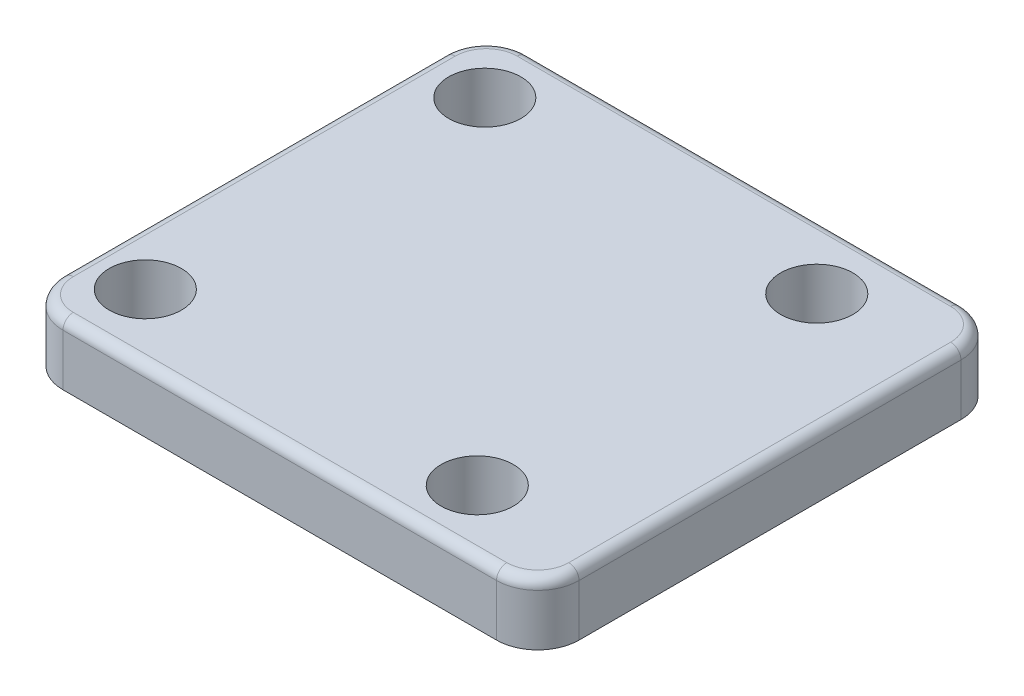
SolidWorks part; units mm, degrees
ref_plane "Front Plane" through (0, 0, 0) normal (0, 0, 1) x (1, 0, 0)
ref_plane "Top Plane" through (0, 0, 0) normal (0, 1, 0) x (1, 0, 0)
ref_plane "Right Plane" through (0, 0, 0) normal (1, 0, 0) x (0, 0, -1)
sketch "Sketch1" plane through (0, 0, 0) normal (0, 1, 0) x (1, 0, 0)
  line L0 (0, 0) -> (-22, 22.5)
  line L1 (-18, 22.5) -> (24, 22.5)
  line L2 (-22, 18.5) -> (-22, -18.5)
  line L3 (-18, -22.5) -> (24, -22.5)
  line L4 (28, 18.5) -> (28, -18.5)
  circle A0 centre (0, 0) radius 23 construction
  circle A1 centre (-16.0797, 16.4452) radius 3.5
  circle A2 centre (0, 0) radius 23 construction
  circle A3 centre (16.4452, 16.0797) radius 3.5
  circle A4 centre (0, 0) radius 23 construction
  circle A5 centre (16.0797, -16.4452) radius 3.5
  circle A6 centre (0, 0) radius 23 construction
  circle A7 centre (-16.4452, -16.0797) radius 3.5
  arc A8 (-22, -18.5) -> (-18, -22.5) centre (-18, -18.5) ccw
  arc A9 (24, -22.5) -> (28, -18.5) centre (24, -18.5) ccw
  arc A10 (24, 22.5) -> (28, 18.5) centre (24, 18.5) cw
  arc A11 (-18, 22.5) -> (-22, 18.5) centre (-18, 18.5) ccw
  point P4 (-22, 0)
  point P12 (-22, -22.5)
  point P22 (0, 0)
  point P27 (28, 22.5)
  dimension "D4" = 46
  dimension "D5" = 7
  dimension "D7" = 4
  dimension "D1" = 45
  dimension "D2" = 50
  dimension "D3" = 22
  dimension "D6" = 4
extrude "Boss-Extrude1" add sketch "Sketch1" along normal blind 6
fillet "Fillet1" radius 1 8 edges at (-20.8284, 6, -21.3284) (3, 6, -22.5) (26.8284, 6, -21.3284) (28, 6, 0) (26.8284, 6, 21.3284) (3, 6, 22.5) (-20.8284, 6, 21.3284) (-22, 6, 0)
sketch "Sketch2" plane through (0, 0, 0) normal (0, -1, 0) x (1, 0, 0)
  circle A0 centre (0, 0) radius 16
  dimension "D1" = 32
extrude "Boss-Extrude2" add sketch "Sketch2" along normal blind 2
chamfer "Chamfer1" distance 1 angle 45 1 edges at (0, -2, -16)
